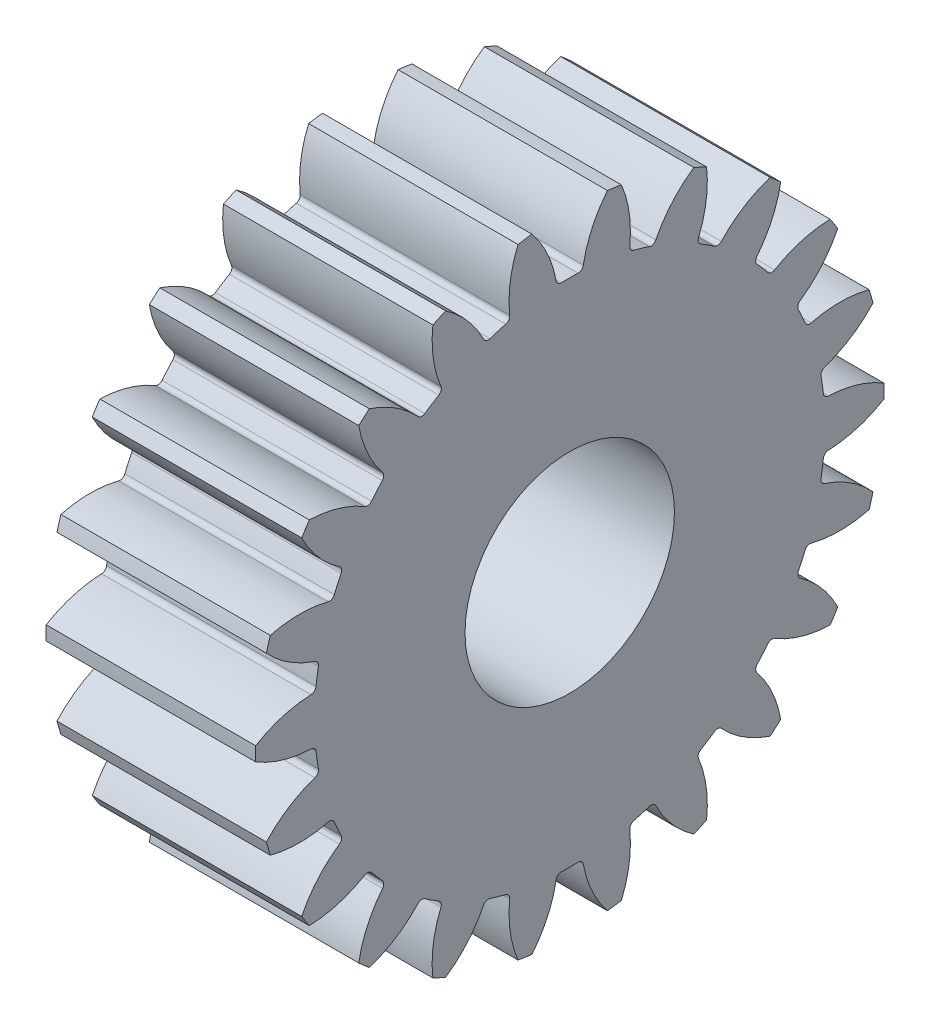
SolidWorks part; units mm, degrees
ref_plane "Plane1" through (0, 0, 0) normal (0, 0, 1) x (1, 0, 0)
ref_plane "Plane2" through (0, 0, 0) normal (0, 1, 0) x (1, 0, 0)
ref_plane "Plane3" through (0, 0, 0) normal (1, 0, 0) x (0, 0, -1)
sketch "HoldingSke" plane through (0, 0, 0) normal (0, 1, 0) x (1, 0, 0)
  line L0 (0, 0) -> (1.8544, -0.7492)
  line L1 (-15, 0) -> (100, 0) construction
  line L2 (0, 0) -> (-2.1039, 2.3779)
  line L3 (0, 0) -> (-11.863, 4.5341)
  line L4 (0, 0) -> (8.0072, 3.2351)
  line L5 (0, 0) -> (-46.8476, -17.4728)
  line L6 (0, 0) -> (-3.3159, -2.2372)
  line L7 (-2.1039, 2.3779) -> (8.6586, 51.2059)
  line L8 (-76.2, 54.61) -> (-75.5, 54.61)
  line L9 (-71.009, 38.7566) -> (-53.1078, 45.2721)
  line L10 (-76.2, 71.12) -> (104.1128, 71.12)
  line L11 (0, 0) -> (-4, 0)
  line L12 (-76.2, 101.6) -> (-76.181, 101.6)
  line L13 (24.9733, 27.94) -> (52.9518, 28.4284)
  line L14 (24.9733, 27.94) -> (24.9743, 27.94)
  line L15 (24.9733, 27.94) -> (100.4006, 29.5858)
  line L16 (-63.627, -0.5) -> (-12.827, -0.5)
  circle A0 centre (0, 0) radius 2
  circle A1 centre (0, 0) radius 4.874
  circle A2 centre (0, 0) radius 37.5
  circle A3 centre (0, 0) radius 2
  dimension "MHD" = 9.748
  dimension "Hub_dia" = 75
  dimension "Bore" = 4
  dimension "MBD" = 4
  dimension "Num_teeth" = 22
  dimension "Pitch" = 2
  dimension "Overall_len" = 50
  dimension "Show_teeth" = 22
  dimension "Thickness" = 4
  dimension "OAL" = 50.0001
  dimension "T_dim" = 0.7
  dimension "Ap" = 20
  dimension "H" = 19.05
  dimension "Pitch_radius" = 180.3128
  dimension "Width" = 4
  dimension "Backlash" = 0.019
  dimension "Addendum_fac" = 1
  dimension "Dedendum_fac" = 1.25
  dimension "Clearance_fac" = 0.25
  dimension "Dedendum_add" = 0.001
  dimension "Module" = 0.5
sketch "BasProSke" plane through (0, 0, 0) normal (0, 1, 0) x (1, 0, 0)
  line L0 (-10, 0) -> (60, 0) construction
  line L1 (0, 0) -> (0, 6)
  line L2 (0, 0) -> (4, 0)
  line L3 (4, 0) -> (4, 6)
  line L4 (4, 6) -> (0, 6)
  dimension "Thickness" = 4
  dimension "Diameter" = 12
revolve "Base-Revolve" add sketch "BasProSke" angle 360 about L0
sketch "TooCutSke" plane through (0, 0, 0) normal (1, 0, 0) x (0, 0, -1)
  line L1 (0, 0) -> (0, 107) construction
  line L2 (0, 0) -> (-0.4256, 5.4835) construction
  line L3 (0, 0) -> (-1.5621, 10.8648) construction
  line L4 (-0.4256, 5.4835) -> (-0.7811, 5.4324) construction
  arc A0 (0.2454, 4.8678) -> (-0.2454, 4.8678) centre (0, 0) ccw
  arc A1 (0.7402, 5.9798) -> (-0.7402, 5.9798) centre (0, 0) ccw
  circle A2 centre (0, 0) radius 5.5 construction
  circle A3 centre (0, 0) radius 5.1683 construction
  arc A4 (-0.2454, 4.8678) -> (-0.7402, 5.9798) centre (-2.4244, 4.5644) ccw
  arc A5 (0.7402, 5.9798) -> (0.2454, 4.8678) centre (2.4244, 4.5644) ccw
  dimension "Root_dia" = 9.748
  dimension "Overcut_dia" = 12.0508
  dimension "Pitch_dia" = 11
  dimension "Base_dia" = 10.3366
  dimension "Flank_rad" = 2.2
  dimension "Half_ang" = 8.182
  dimension "Half_CT" = 0.3591
extrude "ToothCut" cut sketch "TooCutSke" along normal through all
fillet "Breaks" [suppressed] radius 0.01
fillet "RootFillets" [suppressed] radius 0.126
pattern_circular "TeethCuts" count 22 every 16.364 about axis through (-10, 0, 0) along (1, 0, 0) of "ToothCut", "RootFillets", "Breaks"
sketch "HubNeaOneSke" plane through (0, 0, 0) normal (-1, 0, 0) x (0, 0, 1)
  circle A0 centre (0, 0) radius 4.874
  dimension "Diameter" = 9.748
extrude "HubNearOne" [suppressed] add sketch "HubNeaOneSke" along normal blind 46.0001
sketch "HubNeaBotSke" plane through (0, 0, 0) normal (-1, 0, 0) x (0, 0, 1)
  circle A0 centre (0, 0) radius 4.874
  dimension "Diameter" = 9.748
extrude "HubNearBoth" [suppressed] add sketch "HubNeaBotSke" along normal blind 23
ref_plane "FarPln" through (4, 0, 0) normal (1, 0, 0) x (0, 0, -1)
sketch "HubFarSke" plane through (4, 0, 0) normal (1, 0, 0) x (0, 0, -1)
  circle A0 centre (0, 0) radius 4.874
  dimension "Diameter" = 9.748
extrude "HubFar" [suppressed] add sketch "HubFarSke" along normal blind 23
sketch "BorSke" plane through (0, 0, 0) normal (1, 0, 0) x (0, 0, -1)
  circle A0 centre (0, 0) radius 2
  dimension "Diameter" = 4
extrude "Bore" cut sketch "BorSke" along normal mid plane 100.0001
sketch "KeySke" plane through (0, 0, 0) normal (1, 0, 0) x (0, 0, -1)
  line L0 (-0.8, 0) -> (-0.8, 2.7)
  line L1 (-0.8, 2.7) -> (0.8, 2.7)
  line L2 (0.8, 2.7) -> (0.8, 0)
  line L3 (0, 0) -> (0, 34) construction
  line L4 (-0.8, 0) -> (0.8, 0)
  dimension "Offset" = 2.7
  dimension "Width" = 1.6
extrude "Keyway" [suppressed] cut sketch "KeySke" along normal mid plane 100.0001
pattern_circular "Keyway2" [suppressed] count 2 every 90 about axis through (-10, 0, 0) along (1, 0, 0)
fillet "Fillet1" radius 0.1 44 edges at (2, 4.6015, -1.6069) (2, 4.7398, -1.1359) (2, 3.9624, -2.8382) (2, 4.2278, -2.4253) (2, 3.0023, -3.8396) (2, 3.3732, -3.5181) (2, 1.7989, -4.5299) (2, 2.2454, -4.326) (2, 0.4498, -4.8532) (2, 0.9357, -4.7833) (2, -0.9357, -4.7833) (2, -0.4498, -4.8532) (2, -2.2454, -4.326) (2, -1.7989, -4.5299) (2, -3.3732, -3.5181) (2, -3.0023, -3.8396) (2, -4.2278, -2.4253) (2, -3.9624, -2.8382) (2, -4.7398, -1.1359) (2, -4.6015, -1.6069) (2, -4.8678, 0.2454) (2, -4.8678, -0.2454) (2, -4.6015, 1.6069) (2, -4.7398, 1.1359) (2, -3.9624, 2.8382) (2, -4.2278, 2.4253) (2, -3.0023, 3.8396) (2, -3.3732, 3.5181) (2, -1.7989, 4.5299) (2, -2.2454, 4.326) (2, -0.4498, 4.8532) (2, -0.9357, 4.7833) (2, 0.9357, 4.7833) (2, 0.4498, 4.8532) (2, 2.2454, 4.326) (2, 1.7989, 4.5299) (2, 3.3732, 3.5181) (2, 3.0023, 3.8396) (2, 4.2278, 2.4253) (2, 3.9624, 2.8382) (2, 4.7398, 1.1359) (2, 4.6015, 1.6069) (2, 4.8678, -0.2454) (2, 4.8678, 0.2454)
equation "' \"Module@HoldingSke\" = 6.35"
equation "' \"Num_teeth@HoldingSke\" = 12"
equation "' \"Ap@HoldingSke\" =  20"
equation "' \"Ap@HoldingSke\" = 20"
equation "' \"Width@HoldingSke\" = 0.5 * 25.4"
equation "' \"Hub_dia@HoldingSke\"= 1 * 25.4"
equation "' \"Hub_dia@HoldingSke\" = 1 * 25.4"
equation "' \"Overall_len@HoldingSke\" = 1.0 * 25.4"
equation "' \"Bore@HoldingSke\" = 0.75 * 25.4"
equation "' \"T_dim@HoldingSke\" = 0.1 * 25.4"
equation "' \"Width@KeySke\" = 0.25 * 25.4"
equation "' \"Show_teeth@HoldingSke\" = 13"
equation "' \"Backlash@HoldingSke\" = 0.009 * 25.4"
equation "' \"Addendum_fac@HoldingSke\" = 1.0"
equation "' \"Dedendum_fac@HoldingSke\" = 1.25"
equation "' \"Dedendum_add@HoldingSke\" = 0.00005 * 25.4"
equation "' \"Clearance_fac@HoldingSke\" = 0.25"
equation "\"Pitch@HoldingSke\" = 1 / \"Module@HoldingSke\""
equation "\"Overcut_dia@TooCutSke\" = (\"Num_teeth@HoldingSke\" + 2 * \"Addendum_fac@HoldingSke\") / \"Pitch@HoldingSke\" + 0.002 * 25.4"
equation "\"Pitch_dia@TooCutSke\" = \"Num_teeth@HoldingSke\" / \"Pitch@HoldingSke\""
equation "\"Base_dia@TooCutSke\" = \"Num_teeth@HoldingSke\" / \"Pitch@HoldingSke\" * cos((\"Ap@HoldingSke\"  * 3.14159265 / 180))"
equation "\"Root_dia@TooCutSke\" = (\"Num_teeth@HoldingSke\" + 2) / \"Pitch@HoldingSke\" - 2 * (\"Addendum_fac@HoldingSke\" + \"Dedendum_fac@HoldingSke\") / \"Pitch@HoldingSke\" - \"Dedendum_add@HoldingSke\" * 2"
equation "\"Half_ang@TooCutSke\" = 180 / \"Num_teeth@HoldingSke\""
equation "\"Half_CT@TooCutSke\" = \"Num_teeth@HoldingSke\" / \"Pitch@HoldingSke\" * sin((3.14159265 / 2 / \"Num_teeth@HoldingSke\")) / 2 - 7 * \"Backlash@HoldingSke\" / 4"
equation "\"Flank_rad@TooCutSke\" = \"Num_teeth@HoldingSke\" / \"Pitch@HoldingSke\" / 5"
equation "\"Radius@RootFillets\" = \"Clearance_fac@HoldingSke\" / \"Pitch@HoldingSke\" + \"Dedendum_add@HoldingSke\""
equation "\"Break_rad@Breaks\" = 0.02 / \"Pitch@HoldingSke\""
equation "\"Thickness@HoldingSke\" = \"Width@HoldingSke\""
equation "\"OAL@HoldingSke\" = \"Thickness@HoldingSke\""
equation "\"MHD@HoldingSke\" = (\"Num_teeth@HoldingSke\" + 2) / \"Pitch@HoldingSke\" - 2 * (\"Addendum_fac@HoldingSke\" + \"Dedendum_fac@HoldingSke\")  / \"Pitch@HoldingSke\" - \"Dedendum_add@HoldingSke\" * 2"
equation "\"MBD@HoldingSke\" = (\"Num_teeth@HoldingSke\" + 2) / \"Pitch@HoldingSke\" - 2 * (\"Addendum_fac@HoldingSke\" + \"Dedendum_fac@HoldingSke\")  / \"Pitch@HoldingSke\" - \"Dedendum_add@HoldingSke\" * 2 - 0.002 * 25.4"
equation "\"MHD@HoldingSke\" = ((sgn( \"MHD@HoldingSke\" - \"Hub_dia@HoldingSke\" )-1)*( \"MHD@HoldingSke\" - \"Hub_dia@HoldingSke\" ))/-2+ \"Hub_dia@HoldingSke\""
equation "\"MBD@HoldingSke\" = ((sgn( \"MBD@HoldingSke\" - \"Bore@HoldingSke\" )-1)*( \"MBD@HoldingSke\" - \"Bore@HoldingSke\" ))/-2+ \"Bore@HoldingSke\""
equation "\"OAL@HoldingSke\" = ((sgn( \"OAL@HoldingSke\" - \"Overall_len@HoldingSke\" )+1)*( \"OAL@HoldingSke\" - \"Overall_len@HoldingSke\" ))/2 + \"Overall_len@HoldingSke\" + 0.000002 * 25.4"
equation "\"Num_teeth@TeethCuts\" = int( \"Show_teeth@HoldingSke\" ) + 1"
equation "\"Num_teeth@TeethCuts\" = ((sgn( \"Num_teeth@TeethCuts\" - \"Num_teeth@HoldingSke\" )-1)*( \"Num_teeth@TeethCuts\" - \"Num_teeth@HoldingSke\" ))/-2+ \"Num_teeth@HoldingSke\""
equation "\"Num_teeth@TeethCuts\" = ((sgn( \"Num_teeth@TeethCuts\" - 2.0)+1)*( \"Num_teeth@TeethCuts\" - 2.0))/2 +2.0"
equation "\"Angle@TeethCuts\" = 360.0 / \"Num_teeth@HoldingSke\""
equation "\"Diameter@BasProSke\" = (\"Num_teeth@HoldingSke\" + 2 * \"Addendum_fac@HoldingSke\") / \"Pitch@HoldingSke\""
equation "\"Thickness@BasProSke\"  = \"Thickness@HoldingSke\""
equation "' \"Fillet_rad@BasProSke\" =  \"Thickness@HoldingSke\" * 0.05"
equation "' \"Fillet_rad@BasProSke\" = \"Thickness@HoldingSke\" * 0.05"
equation "\"MHD@HoldingSke\" = ((sgn( \"MHD@HoldingSke\" - \"Root_dia@TooCutSke\" )-1)*( \"MHD@HoldingSke\" - \"Root_dia@TooCutSke\" ))/-2+ \"Root_dia@TooCutSke\""
equation "\"Diameter@HubNeaOneSke\" = \"MHD@HoldingSke\""
equation "\"Length@HubNearOne\" = \"OAL@HoldingSke\" - \"Thickness@BasProSke\""
equation "\"Diameter@HubNeaBotSke\" = \"MHD@HoldingSke\""
equation "\"Length@HubNearBoth\" = ( \"OAL@HoldingSke\" - \"Thickness@BasProSke\" ) / 2.0"
equation "\"Thickness@FarPln\" = \"Thickness@BasProSke\""
equation "\"Diameter@HubFarSke\" = \"MHD@HoldingSke\""
equation "\"Length@HubFar\" = ( \"OAL@HoldingSke\" - \"Thickness@BasProSke\" ) / 2.0"
equation "\"Diameter@BorSke\" = \"MBD@HoldingSke\""
equation "\"D1@Bore\" = \"OAL@HoldingSke\" * 2.0"
equation "\"D1@Keyway\" = \"OAL@HoldingSke\" * 2.0"
equation "\"Offset@KeySke\" = \"T_dim@HoldingSke\" + \"MBD@HoldingSke\" / 2.0"
